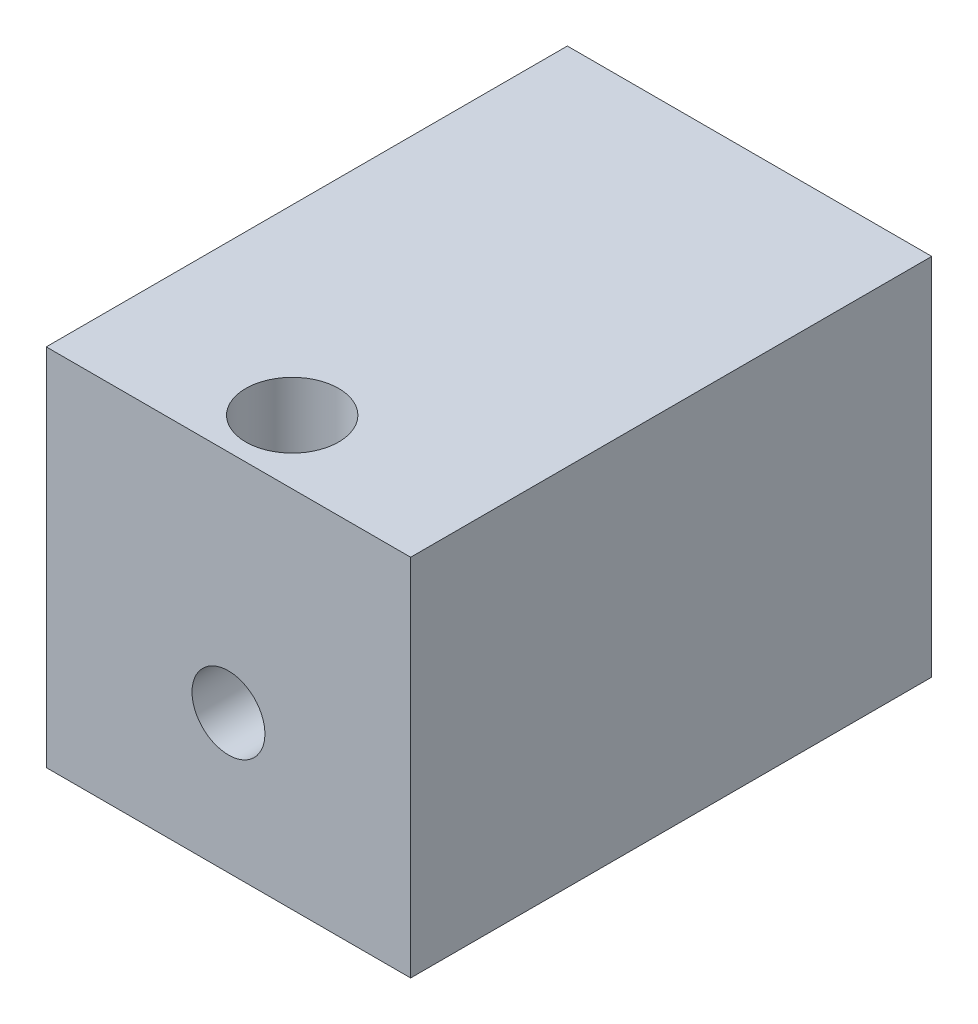
SolidWorks part; units mm, degrees
ref_plane "Ebene vorne" through (0, 0, 0) normal (0, 0, 1) x (1, 0, 0)
ref_plane "Ebene oben" through (0, 0, 0) normal (0, 1, 0) x (1, 0, 0)
ref_plane "Ebene rechts" through (0, 0, 0) normal (1, 0, 0) x (0, 0, -1)
sketch "Sketch1" plane through (0, 0, 0) normal (0, 1, 0) x (1, 0, 0)
  line L1 (0, 0) -> (20, 0)
  line L2 (0, 0) -> (0, 28.6)
  line L3 (0, 28.6) -> (20, 28.6)
  line L4 (20, 0) -> (20, 28.6)
  dimension "D1" = 28.6
  dimension "D2" = 20
extrude "Boss-Extrude1" add sketch "Sketch1" along normal blind 20
fillet "Chamfer1" [suppressed] radius 6
sketch "Sketch2" plane through (0, 0, 0) normal (0, -1, 0) x (1, 0, 0)
  line L0 (20, -18.6) -> (0, -18.6) construction
  line L3 (20, -28.6) -> (0, -28.6) construction
  circle A0 centre (10, -18.6) radius 7.6
  dimension "D1" = 15.2
  dimension "D2" = 10
extrude "Cut-Extrude1" cut sketch "Sketch2" against normal blind 13
sketch "Sketch3" plane through (0, 0, -28.6) normal (0, 0, -1) x (-1, 0, 0)
  line L0 (-10, 0) -> (-10, 14) construction
  line L1 (-20, 0) -> (0, 0) construction
  line L3 (-17.6, 13) -> (-2.4, 13) construction
  line L4 (-17.6, 13) -> (-2.4, 13) construction
  circle A0 centre (-10, 7.6) radius 2
  dimension "D1" = 4
  dimension "D2" = 5.4
extrude "Cut-Extrude2" cut sketch "Sketch3" against normal up to surface (28.6 mm away) up to face at (10, 10, 0)
sketch "Skizze1" plane through (0, 20, 0) normal (0, 1, 0) x (1, 0, 0)
  line L0 (0, 0) -> (20, 0) construction
  line L1 (10, 0) -> (10, 3.5) construction
  circle A0 centre (10, 3.5) radius 2.55
  dimension "D1" = 5.1
  dimension "D2" = 3.5
extrude "Schnitt-Linear austragen1" cut sketch "Skizze1" against normal blind 8
